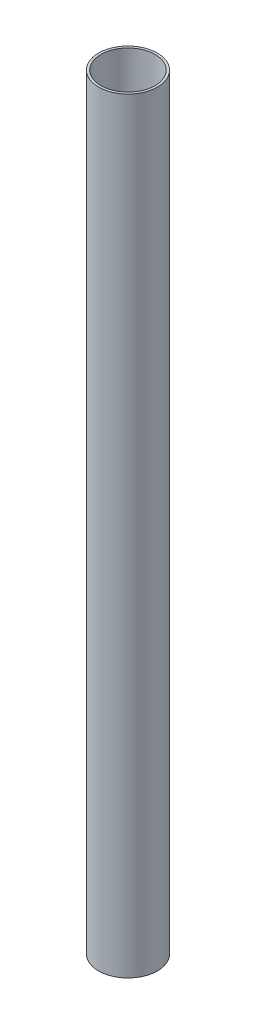
SolidWorks part; units mm, degrees
other "Marca1"
sketch "Croquis2" plane through (25, 650, 25) normal (0, 0.8246, 0.5657) x (1, 0, 0)
material "ASTM A36 Acero"
ref_plane "Alzado" through (0, 0, 0) normal (0, 0, 1) x (1, 0, 0)
ref_plane "Planta" through (0, 0, 0) normal (0, 1, 0) x (1, 0, 0)
ref_plane "Vista lateral" through (0, 0, 0) normal (1, 0, 0) x (0, 0, -1)
sketch "Croquis1" plane through (0, 0, 0) normal (0, 1, 0) x (1, 0, 0)
  circle A0 centre (0, 0) radius 25
  circle A1 centre (0, 0) radius 23
  dimension "D1" = 50
  dimension "D2" = 46
extrude "Saliente-Extruir1" add sketch "Croquis1" along normal blind 650
